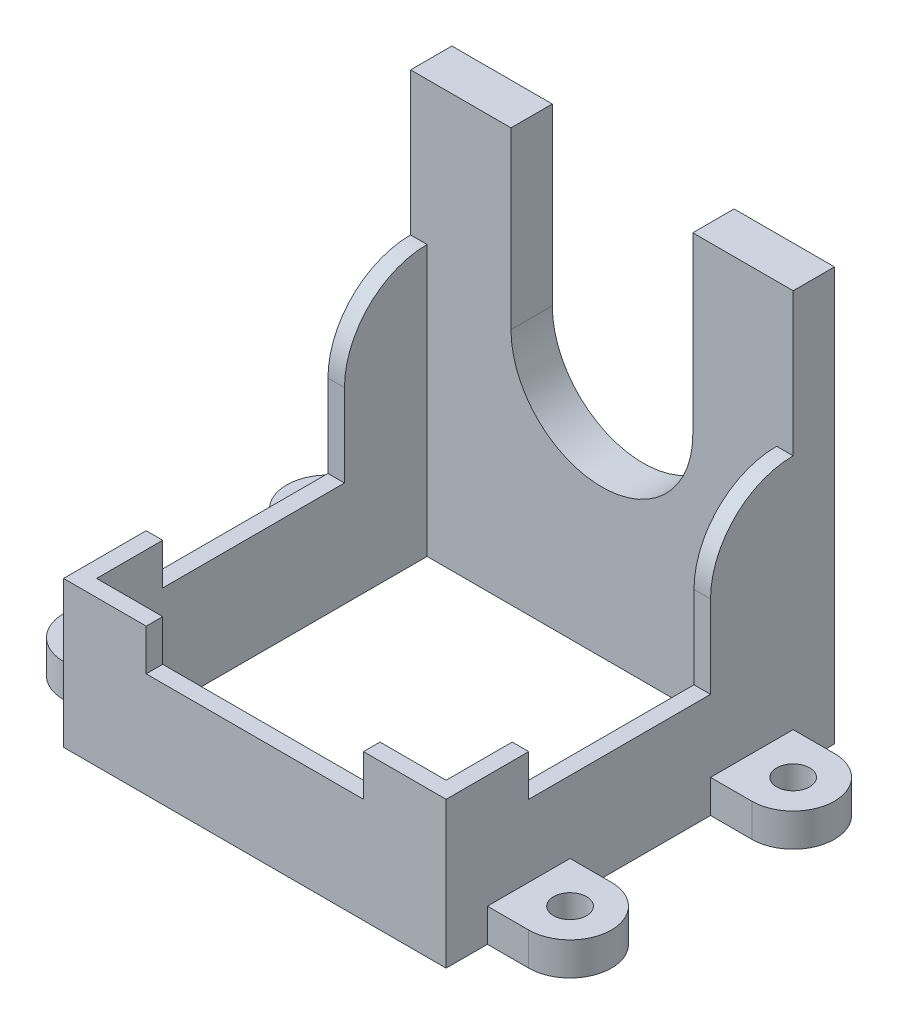
SolidWorks part; units mm, degrees
ref_plane "前基準面" through (0, 0, 0) normal (0, 0, 1) x (1, 0, 0)
ref_plane "上基準面" through (0, 0, 0) normal (0, 1, 0) x (1, 0, 0)
ref_plane "右基準面" through (0, 0, 0) normal (1, 0, 0) x (0, 0, -1)
sketch "草圖1" plane through (0, 0, 0) normal (0, 1, 0) x (1, 0, 0)
  line L1 (0, 0) -> (46.3, 0)
  line L2 (0, 0) -> (0, 47)
  line L3 (0, 47) -> (46.3, 47)
  line L4 (46.3, 0) -> (46.3, 47)
  dimension "D1" = 46.3
  dimension "D2" = 47
extrude "填料-伸長1" add sketch "草圖1" along normal blind 50
sketch "草圖2" plane through (0, 50, 0) normal (0, 1, 0) x (1, 0, 0)
  line L0 (0, 47) -> (0, 0) construction
  line L1 (0, 42) -> (46.3, 42)
  line L2 (0, 42) -> (0, 0)
  line L3 (0, 0) -> (46.3, 0)
  line L4 (46.3, 42) -> (46.3, 0)
  dimension "D1" = 5
extrude "除料-伸長1" cut sketch "草圖2" against normal blind 32.3
sketch "草圖3" plane through (0, 17.7, 0) normal (0, 1, 0) x (1, 0, 0)
  line L0 (46.3, 42) -> (0, 42) construction
  line L1 (2, 42) -> (44.3, 42)
  line L2 (2, 42) -> (2, 2)
  line L3 (2, 2) -> (44.3, 2)
  line L4 (44.3, 42) -> (44.3, 2)
  line L5 (46.3, 0) -> (46.3, 42) construction
  line L6 (0, 42) -> (0, 0) construction
  line L7 (0, 0) -> (46.3, 0) construction
  dimension "D1" = 0
  dimension "D2" = 2
  dimension "D3" = 2
  dimension "D4" = 2
extrude "除料-伸長2" cut sketch "草圖3" against normal blind 10
sketch "草圖4" plane through (0, 7.7, 0) normal (0, 1, 0) x (1, 0, 0)
  line L0 (44.3, 2) -> (44.3, 42) construction
  line L1 (2, 42) -> (44.3, 42)
  line L2 (2, 42) -> (2, 5)
  line L3 (2, 5) -> (44.3, 5)
  line L4 (44.3, 42) -> (44.3, 5)
  line L5 (2, 2) -> (44.3, 2) construction
  dimension "D1" = 3
extrude "除料-伸長3" cut sketch "草圖4" against normal through all
sketch "草圖5" plane through (0, 17.7, 0) normal (0, 1, 0) x (1, 0, 0)
  line L0 (0, 42) -> (0, 0) construction
  line L1 (0, 32) -> (2, 32)
  line L2 (0, 32) -> (0, 10)
  line L3 (0, 10) -> (2, 10)
  line L4 (2, 32) -> (2, 10)
  line L5 (2, 42) -> (2, 2) construction
  line L6 (46.3, 42) -> (0, 42) construction
  line L8 (0, 0) -> (46.3, 0) construction
  line L9 (44.3, 2) -> (44.3, 42) construction
  line L10 (44.3, 32) -> (46.3, 32)
  line L11 (44.3, 32) -> (44.3, 10)
  line L12 (44.3, 10) -> (46.3, 10)
  line L13 (46.3, 32) -> (46.3, 10)
  line L14 (46.3, 0) -> (46.3, 42) construction
  line L15 (2, 2) -> (44.3, 2) construction
  line L16 (10, 2) -> (36.3, 2)
  line L17 (10, 2) -> (10, 0)
  line L18 (10, 0) -> (36.3, 0)
  line L19 (36.3, 2) -> (36.3, 0)
  dimension "D1" = 10
  dimension "D2" = 270
  dimension "D3" = 10
  dimension "D4" = 10
  dimension "D5" = 10
  dimension "D6" = 22
  dimension "D7" = 10
extrude "除料-伸長4" cut sketch "草圖5" against normal blind 5
sketch "草圖7" plane through (0, 0, 0) normal (-1, 0, 0) x (0, 0, 1)
  line L0 (-42, 17.7) -> (-42, 50) construction
  line L1 (-42, 22.7) -> (-32, 22.7)
  line L2 (-42, 22.7) -> (-42, 17.7)
  line L3 (-42, 17.7) -> (-32, 17.7)
  line L4 (-32, 22.7) -> (-32, 17.7)
  arc A0 (-42, 32.7) -> (-32, 22.7) centre (-42, 22.7) cw
  line M4 (-32, 17.7) -> (-42, 17.7)
  line M5 (-42, 17.7) -> (-42, 50)
  dimension "D1" = 5
extrude "填料-伸長2" add sketch "草圖7" against normal blind 2 contours A0 L1 M5 | L4 L1 M5 M4
sketch "草圖8" plane through (46.3, 0, 0) normal (1, 0, 0) x (0, 0, -1)
  line L1 (42, 17.7) -> (32, 17.7)
  line L2 (42, 17.7) -> (42, 22.7)
  line L3 (42, 22.7) -> (32, 22.7)
  line L4 (32, 17.7) -> (32, 22.7)
  arc A0 (42, 32.7) -> (32, 22.7) centre (42, 22.7) ccw
  arc A1 (42, 32.7) -> (32, 22.7) centre (42, 22.7) ccw construction
extrude "填料-伸長3" add sketch "草圖8" against normal blind 2
sketch "草圖9" plane through (0, 0, -42) normal (0, 0, 1) x (1, 0, 0)
  line L0 (46.3, 50) -> (0, 50) construction
  line L1 (12.15, 50) -> (34.15, 50)
  line L2 (12.15, 50) -> (12.15, 28.85)
  line L3 (12.15, 28.85) -> (34.15, 28.85)
  line L4 (34.15, 50) -> (34.15, 28.85)
  arc A0 (34.15, 28.85) -> (12.15, 28.85) centre (23.15, 28.85) cw
  line M5 (46.3, 50) -> (0, 50)
  dimension "D1" = 12.15
  dimension "D2" = 12.15
  dimension "D3" = 21.15
extrude "除料-伸長5" cut sketch "草圖9" against normal through all contours A0 L3 | L4 L2 L3 M5
sketch "草圖11" plane through (0, 0, 0) normal (0, -1, 0) x (1, 0, 0)
  line L0 (46.3, 0) -> (46.3, -47) construction
  line L1 (46.3, -5) -> (51.3, -5)
  line L2 (46.3, -5) -> (46.3, -15)
  line L3 (46.3, -15) -> (51.3, -15)
  line L4 (51.3, -5) -> (51.3, -15)
  line L5 (0, 0) -> (46.3, 0) construction
  line L6 (0, -47) -> (0, 0) construction
  line L7 (46.3, -42) -> (51.3, -42)
  line L8 (46.3, -42) -> (46.3, -32)
  line L9 (46.3, -32) -> (51.3, -32)
  line L10 (51.3, -42) -> (51.3, -32)
  line L11 (0, -5) -> (-5, -5)
  line L12 (0, -5) -> (0, -15)
  line L13 (0, -15) -> (-5, -15)
  line L14 (-5, -5) -> (-5, -15)
  line L16 (0, -32) -> (-5, -32)
  line L17 (0, -32) -> (0, -42)
  line L18 (0, -42) -> (-5, -42)
  line L19 (-5, -32) -> (-5, -42)
  arc A0 (51.3, -5) -> (51.3, -15) centre (51.3, -10) cw
  arc A1 (51.3, -32) -> (51.3, -42) centre (51.3, -37) cw
  circle A2 centre (51.3, -10) radius 2
  circle A3 centre (51.3, -37) radius 2
  arc A4 (-5, -15) -> (-5, -5) centre (-5, -10) cw
  circle A5 centre (-5, -10) radius 2
  arc A6 (-5, -42) -> (-5, -32) centre (-5, -37) cw
  circle A7 centre (-5, -37) radius 2
  circle A8 centre (-5, -10) radius 2
  line M11 (0, 0) -> (0, -47)
  line M13 (46.3, -47) -> (46.3, 0)
  dimension "D6" = 5
  dimension "D7" = 10
  dimension "D1" = 5
  dimension "D2" = 10
  dimension "D3" = 5
  dimension "D4" = 10
  dimension "D5" = 5
  dimension "D8" = 10
  dimension "D9" = 5
extrude "填料-伸長4" add sketch "草圖11" against normal blind 4 contours A5 L14 L13 L11 M11 | A5 L14 A4 | A7 L19 L18 L16 M11 | A7 L19 A6 | A2 L4 L1 L3 M13 | A2 L4 A0 | A3 L10 A1 | A3 L10 L9 L7 M13
sketch "草圖12" plane through (0, 0, 0) normal (0, -1, 0) x (1, 0, 0)
  circle A0 centre (-5, -10) radius 2
  dimension "D1" = 5
  dimension "D2" = 5
extrude "除料-伸長6" cut sketch "草圖12" against normal blind 4
scale "縮放比例1" scale about centroid uniform scaling yes scale factor 1.015
